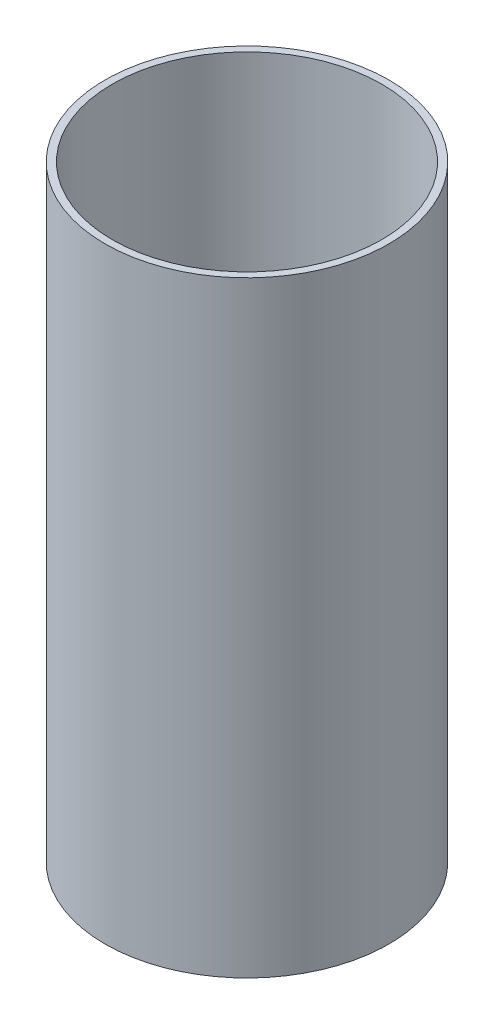
SolidWorks part; units mm, degrees
material "PVC Rigid"
ref_plane "Front Plane" through (0, 0, 0) normal (0, 0, 1) x (1, 0, 0)
ref_plane "Top Plane" through (0, 0, 0) normal (0, 1, 0) x (1, 0, 0)
ref_plane "Right Plane" through (0, 0, 0) normal (1, 0, 0) x (0, 0, -1)
sketch "Sketch1" plane through (0, 0, 0) normal (0, 1, 0) x (1, 0, 0)
  circle A0 centre (0, 0) radius 93.6625
  circle A1 centre (0, 0) radius 88.9
  dimension "D1" = 187.325
  dimension "D2" = 177.8
extrude "Boss-Extrude1" add sketch "Sketch1" along normal mid plane 400.05
